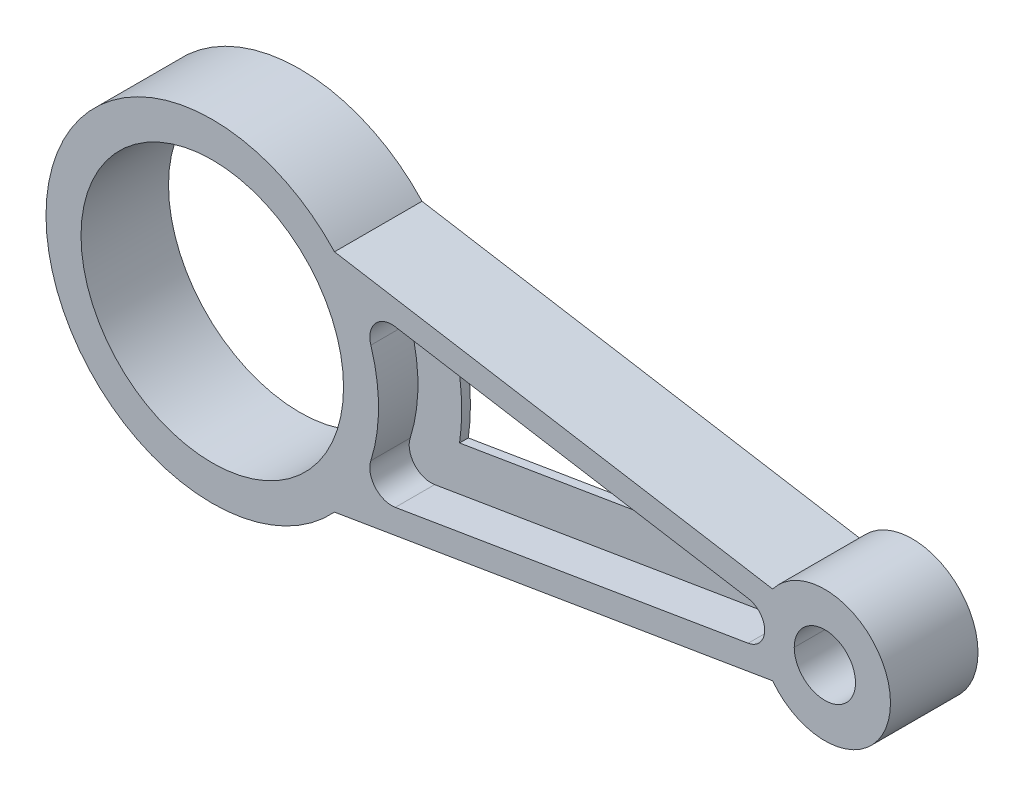
SolidWorks part; units mm, degrees
material "Plain Carbon Steel"
ref_plane "Front Plane" through (0, 0, 0) normal (0, 0, 1) x (1, 0, 0)
ref_plane "Top Plane" through (0, 0, 0) normal (0, 1, 0) x (1, 0, 0)
ref_plane "Right Plane" through (0, 0, 0) normal (1, 0, 0) x (0, 0, -1)
sketch "Sketch1" plane through (0, 0, 0) normal (0, 0, 1) x (1, 0, 0)
  line L0 (0, 0) -> (140, 0) construction
  line L1 (27.9355, 25.7606) -> (128.0638, 9.0844)
  line L2 (27.9355, -25.7606) -> (128.0638, -9.0844)
  circle A0 centre (0, 0) radius 38
  circle A1 centre (140, 0) radius 15
  circle A2 centre (0, 0) radius 30
  circle A3 centre (140, 0) radius 7
  dimension "D1" = 60
  dimension "D2" = 76
  dimension "D3" = 14
  dimension "D4" = 30
  dimension "D5" = 140
extrude "Boss-Extrude1" add sketch "Sketch1" along normal mid plane 20
sketch "Sketch2" plane through (0, 0, 10) normal (0, 0, 1) x (1, 0, 0)
  line L0 (0, 0) -> (174.5593, 0) construction
  line L1 (41.8286, 17.871) -> (122.4784, 4.4389)
  line L2 (122.4784, -4.4389) -> (41.8286, -17.871)
  line L7 (27.9355, 25.7606) -> (128.0638, 9.0844) construction
  arc A0 (36.2389, 11.4344) -> (36.2389, -11.4344) centre (0, 0) cw
  arc A1 (36.2389, 11.4344) -> (41.8286, 17.871) centre (41.0071, 12.9389) cw
  arc A2 (36.2389, -11.4344) -> (41.8286, -17.871) centre (41.0071, -12.9389) ccw
  arc A3 (122.4784, 4.4389) -> (122.4784, -4.4389) centre (121.7391, 0) cw
  circle A5 centre (0, 0) radius 30 construction
  dimension "D1" = 5
  dimension "D2" = 4.5
  dimension "D3" = 8
  dimension "D4" = 5.5
extrude "Cut-Extrude1" cut sketch "Sketch2" against normal blind 9
mirror "Mirror1" about plane through (0, 0, 0) normal (0, 0, 1) of "Cut-Extrude1"
split line "Split Line1"
sketch "Sketch3" plane through (0, 0, 1) normal (0, 0, 1) x (1, 0, 0)
  line L11 (47.5179, -6.7857) -> (88.2609, 0)
  line L12 (88.2609, 0) -> (47.5179, 6.7857)
  line L13 (47.5179, -6.7857) -> (88.2609, 0)
  line L14 (88.2609, 0) -> (47.5179, 6.7857)
  arc A16 (47.5179, -6.7857) -> (47.5179, 6.7857) centre (0, 0) ccw
  arc A17 (47.5179, -6.7857) -> (47.5179, 6.7857) centre (0, 0) ccw
  dimension "D1" = 10
extrude "Cut-Extrude2" cut sketch "Sketch3" against normal through all
